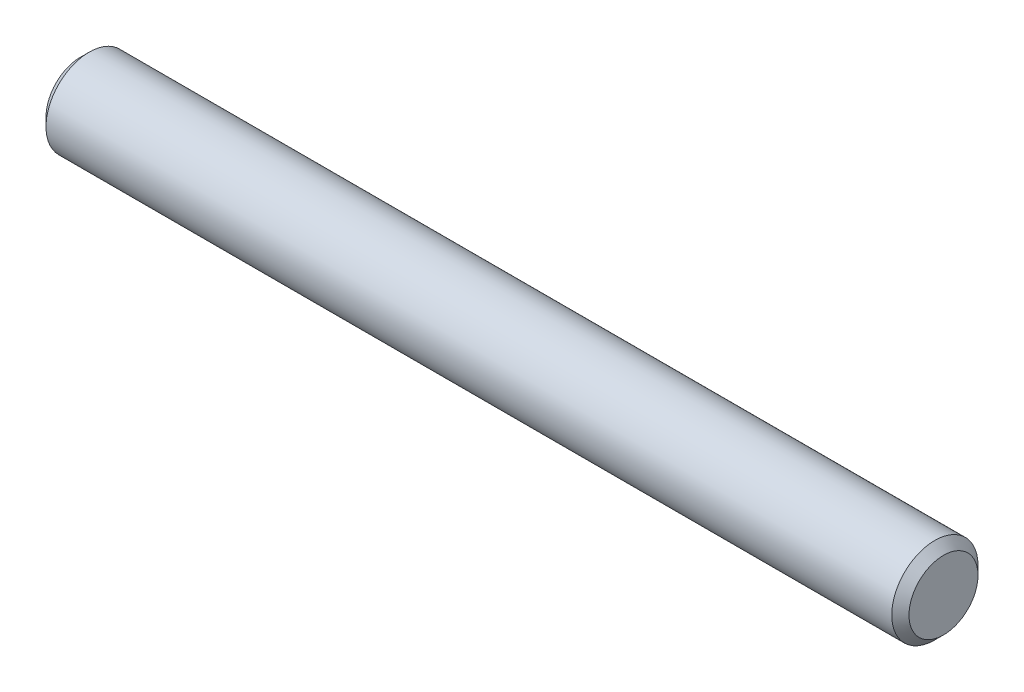
SolidWorks part; units mm, degrees
ref_plane "Front" through (0, 0, 0) normal (0, 0, 1) x (1, 0, 0)
ref_plane "Top" through (0, 0, 0) normal (0, 1, 0) x (1, 0, 0)
ref_plane "Right" through (0, 0, 0) normal (1, 0, 0) x (0, 0, -1)
sketch "Sketch1" plane through (0, 0, 0) normal (0, 0, 1) x (1, 0, 0)
  line L0 (-7.9375, 0) -> (7.9375, 0) construction
  line L1 (7.9375, 0.7937) -> (7.9375, -0.7937) construction
  line L2 (-7.9375, 0.7937) -> (-7.9375, -0.7937) construction
  dimension "Length" = 15.875
  dimension "Diameter" = 1.5875
sketch "Sketch2" plane through (0, 0, 0) normal (1, 0, 0) x (0, 0, -1)
  circle A0 centre (0, 0) radius 0.7937
extrude "Extrude1" add sketch "Sketch2" against normal up to vertex (7.9375 mm away) and the other way up to vertex (7.9375 mm away) up to point (-7.9375, 0.7937, 0) other way up to point (7.9375, 0.7937, 0)
chamfer "Chamfer1" distance 0.1588 angle 45 2 edges at (7.9375, 0, -0.7937) (-7.9375, 0, -0.7937)
equation "\"D1@Chamfer1\" = \"Diameter@Sketch1\"*.1"
